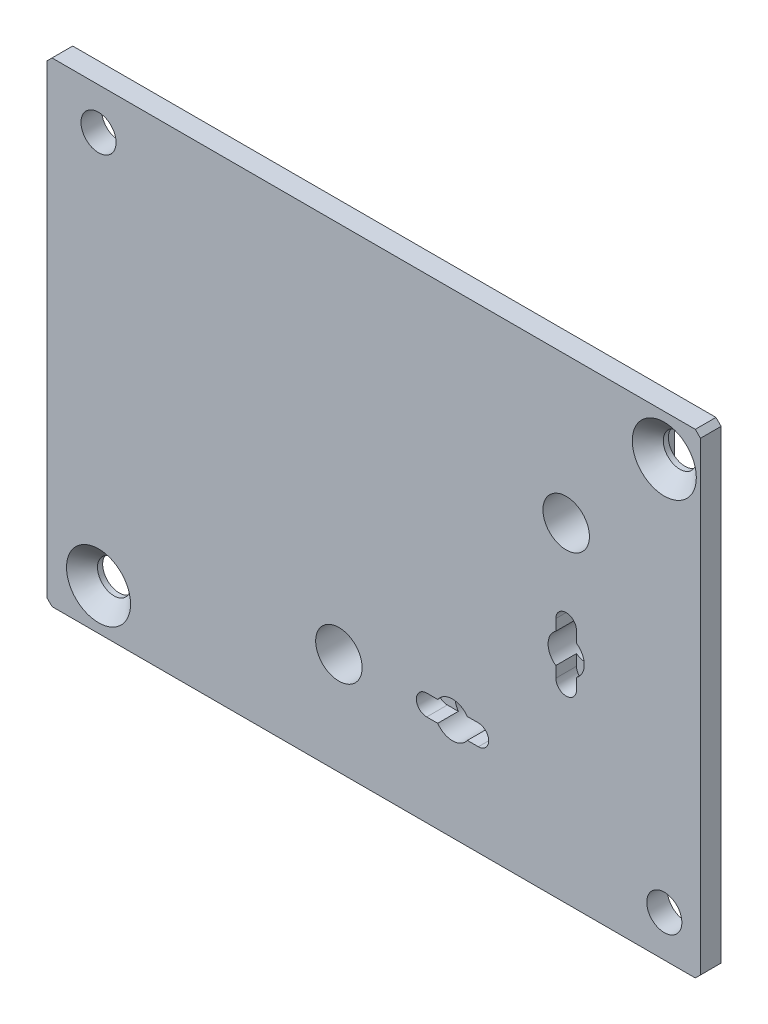
SolidWorks part; units mm, degrees
material "3.1645 (EN-AW 2030)"
ref_plane "Přední rovina" through (0, 0, 0) normal (0, 0, 1) x (1, 0, 0)
ref_plane "Horní rovina" through (0, 0, 0) normal (0, 1, 0) x (1, 0, 0)
ref_plane "Pravá rovina" through (0, 0, 0) normal (1, 0, 0) x (0, 0, -1)
sketch "Skica1" plane through (0, 0, 0) normal (0, 0, 1) x (1, 0, 0)
  line L0 (-318.8797, -20) -> (-269.6099, -20) construction
  line L1 (-318.8797, 20) -> (-318.8797, -20) construction
  line L2 (-269.6099, 20) -> (-318.8797, 20) construction
  line L3 (-269.6099, -20) -> (-269.6099, 20) construction
  line L4 (-318.8797, -20) -> (-269.6099, -20)
  line L5 (-318.8797, 20) -> (-318.8797, -20)
  line L6 (-269.6099, 20) -> (-318.8797, 20)
  line L7 (-269.6099, -20) -> (-269.6099, 20)
extrude "Přidat vysunutím1" add sketch "Skica1" against normal up to vertex (2 mm away)
chamfer "Zkosení1" distance 0.5 angle 45 4 edges at (-294.2448, -20, -2) (-269.6099, 0, -2) (-294.2448, 20, -2) (-318.8797, 0, -2)
sketch "Skica2" plane through (0, 0, -2) normal (0, 0, -1) x (-1, 0, 0)
  point P0 (279.8778, -13.1125)
  point P2 (273.3419, -13.1125)
  point P4 (276.6099, -13.1125)
ref_plane "Rovina1" through (0, -13.1125, 0) normal (0, -1, 0) x (-1, 0, 0)
sketch "Skica3" plane through (0, -13.1125, 0) normal (0, -1, 0) x (-1, 0, 0)
  line L2 (273.3419, 2) -> (276.6099, 0.1132)
  line L3 (276.6099, 0.1132) -> (276.6099, 2)
  line L6 (273.3419, 2) -> (276.6099, 2)
revolve "Odebrat rotací2" cut sketch "Skica3" angle 360 about L3
sketch "Skica4" plane through (0, 0, 0) normal (0, 0, 1) x (1, 0, 0)
  line L0 (-263.6099, 23) -> (-326.8797, 23) construction
  line L1 (-263.6099, -23) -> (-263.6099, 23) construction
  line L2 (-326.8797, -23) -> (-263.6099, -23) construction
  line L3 (-326.8797, 23) -> (-326.8797, -23) construction
  line L4 (-263.6099, 23) -> (-326.8797, 23)
  line L5 (-263.6099, -23) -> (-263.6099, 23)
  line L6 (-326.8797, -23) -> (-263.6099, -23)
  line L7 (-326.8797, 23) -> (-326.8797, -23)
extrude "Přidat vysunutím2" add sketch "Skica4" along normal blind 2 contours L4 L7 L6 L5
sketch "Skica6" plane through (0, 0, 2) normal (0, 0, 1) x (1, 0, 0)
  line L1 (-321.8797, -19) -> (-267.1099, -19) construction
  line L2 (-321.8797, -19) -> (-321.8797, 19) construction
  line L3 (-321.8797, 19) -> (-267.1099, 19) construction
  line L4 (-267.1099, -19) -> (-267.1099, 19) construction
  circle A0 centre (-321.8797, -19) radius 1.525 construction
  circle A1 centre (-321.8797, -19) radius 1.525
  circle A2 centre (-267.1099, 19) radius 1.525 construction
  circle A3 centre (-267.1099, 19) radius 1.525
hole_wizard "Kuželové zahloubení pro M3 šroubu se zápustnou hlavou plochou1" positions "3DSkica1" profile "Skica7" countersink size "M3" standard "ISO" end condition up to next
sketch3d "3DSkica1"
  point P0 (-321.8797, -19, 2)
  point P3 (-267.1099, 19, 2)
sketch "Skica7" plane through (-321.8797, -19, 2) normal (1, 0, 0) x (0, -1, 0)
  line L0 (0, 0) -> (0, 2)
  line L1 (0, 2) -> (1.6, 2)
  line L2 (1.6, 2) -> (1.6, 1.5)
  line L3 (1.6, 1.5) -> (3.1, 0)
  line L5 (3.1, 0) -> (0, 0)
  line L6 (-1.6, 1.5) -> (-3.1, 0) construction
  line L11 (0, -6.35) -> (0, 107.95) construction
  dimension "Průměr díry skrz" = 3.2
  dimension "Hloubka díry skrz" = 2
  dimension "Průměr blíz. kuž. zahloubení" = 6.2
  dimension "Úhel blíz. kuž. zahloubení" = 90
hole_wizard "Ø3.4 (3.4) průměr díry1" positions "3DSkica2" profile "Skica8" hole size "Ø3.4" standard "ISO" end condition up to next
sketch3d "3DSkica2"
  point P0 (-267.1099, -19, 2)
  point P3 (-321.8797, 19, 2)
sketch "Skica8" plane through (-267.1099, -19, 2) normal (1, 0, 0) x (0, -1, 0)
  line L0 (0, 0) -> (0, 2)
  line L1 (0, 2) -> (1.7, 2)
  line L2 (1.7, 2) -> (1.7, 0)
  line L5 (1.7, 0) -> (0, 0)
  line L11 (0, -6.35) -> (0, 107.95) construction
  dimension "Průměr díry skrz" = 3.4
  dimension "Hloubka díry skrz" = 2
sketch "Skica9" plane through (0, 0, 2) normal (0, 0, 1) x (1, 0, 0)
  line L0 (-290.1099, -14.1125) -> (-285.1099, -14.1125)
  line L1 (-285.1099, -12.1125) -> (-290.1099, -12.1125)
  line L2 (-277.6099, 0.3875) -> (-277.6099, -4.6125)
  line L3 (-275.6099, -4.6125) -> (-275.6099, 0.3875)
  arc A0 (-290.1099, -12.1125) -> (-290.1099, -14.1125) centre (-290.1099, -13.1125) ccw construction
  arc A1 (-290.1099, -12.1125) -> (-290.1099, -14.1125) centre (-290.1099, -13.1125) ccw
  arc A2 (-285.1099, -14.1125) -> (-285.1099, -12.1125) centre (-285.1099, -13.1125) ccw construction
  arc A3 (-285.1099, -14.1125) -> (-285.1099, -12.1125) centre (-285.1099, -13.1125) ccw
  arc A4 (-275.6099, 0.3875) -> (-277.6099, 0.3875) centre (-276.6099, 0.3875) ccw construction
  arc A5 (-277.6099, -4.6125) -> (-275.6099, -4.6125) centre (-276.6099, -4.6125) ccw construction
  arc A6 (-275.6099, 0.3875) -> (-277.6099, 0.3875) centre (-276.6099, 0.3875) ccw
  arc A7 (-277.6099, -4.6125) -> (-275.6099, -4.6125) centre (-276.6099, -4.6125) ccw
extrude "Odebrat vysunutím1" cut sketch "Skica9" against normal blind 2
hole_wizard "Ø3.5 (3.5) průměr díry1" positions "3DSkica3" profile "Skica10" hole size "Ø3.5" standard "ISO" end condition up to next
sketch3d "3DSkica3"
  circle A0 centre (-287.6099, -13.1125, -4) radius 1.75 construction
  circle A1 centre (-276.6099, -2.1125, -4) radius 1.75 construction
  point P0 (-287.6099, -13.1125, 2)
  point P2 (-276.6099, -2.1125, 2)
  point P7 (-287.6099, -13.1125, -5.75)
  point P11 (-276.6099, -2.1125, -5.75)
sketch "Skica10" plane through (-287.6099, -13.1125, 2) normal (1, 0, 0) x (0, -1, 0)
  line L0 (0, 0) -> (0, 4)
  line L1 (0, 4) -> (1.75, 4)
  line L2 (1.75, 4) -> (1.75, 0)
  line L5 (1.75, 0) -> (0, 0)
  line L11 (0, -6.35) -> (0, 107.95) construction
  dimension "Průměr díry skrz" = 3.5
  dimension "Hloubka díry skrz" = 4
hole_wizard "Ø4.5 (4.5) průměr díry1" positions "3DSkica4" profile "Skica11" hole size "Ø4.5" standard "ISO" end condition up to next
sketch3d "3DSkica4"
  point P0 (-276.6099, 8.8875, 2)
  point P2 (-298.6099, -13.1125, 2)
sketch "Skica11" plane through (-276.6099, 8.8875, 2) normal (1, 0, 0) x (0, -1, 0)
  line L0 (0, 0) -> (0, 4)
  line L1 (0, 4) -> (2.25, 4)
  line L2 (2.25, 4) -> (2.25, 0)
  line L5 (2.25, 0) -> (0, 0)
  line L11 (0, -6.35) -> (0, 107.95) construction
  dimension "Průměr díry skrz" = 4.5
  dimension "Hloubka díry skrz" = 4
ref_plane "Rovina2" through (-290.1099, 0, 0) normal (-1, 0, 0) x (0, 0, 1)
sketch "Skica12" plane through (-290.1099, 0, 0) normal (-1, 0, 0) x (0, 0, 1)
  line L0 (0, -14.1125) -> (0, -12.1125) construction
  line L1 (0, -14.1125) -> (0, -12.1125)
  line L3 (0.75, -12.1125) -> (0.75, -14.1125)
  line L4 (0, -12.1125) -> (2, -12.1125) construction
  line L5 (0, -14.1125) -> (2, -14.1125) construction
  circle A0 centre (0.75, -13.1125) radius 0.75
  dimension "D1" = 0.75
ref_plane "Rovina3" through (0, -4.6125, 0) normal (0, -1, 0) x (-1, 0, 0)
sketch "Skica13" plane through (0, -4.6125, 0) normal (0, -1, 0) x (-1, 0, 0)
  line L0 (275.6099, 0) -> (277.6099, 0) construction
  line L1 (275.6099, 0) -> (277.6099, 0)
  line L5 (276.6099, 0) -> (276.6099, -2.3448)
  circle A0 centre (276.6099, -0.75) radius 0.75
  dimension "D1" = 1.5
chamfer "Zkosení2" distance 0.5 angle 45 4 edges at (-326.8797, -23, 1) (-326.8797, 23, 1) (-263.6099, -23, 1) (-263.6099, 23, 1)
